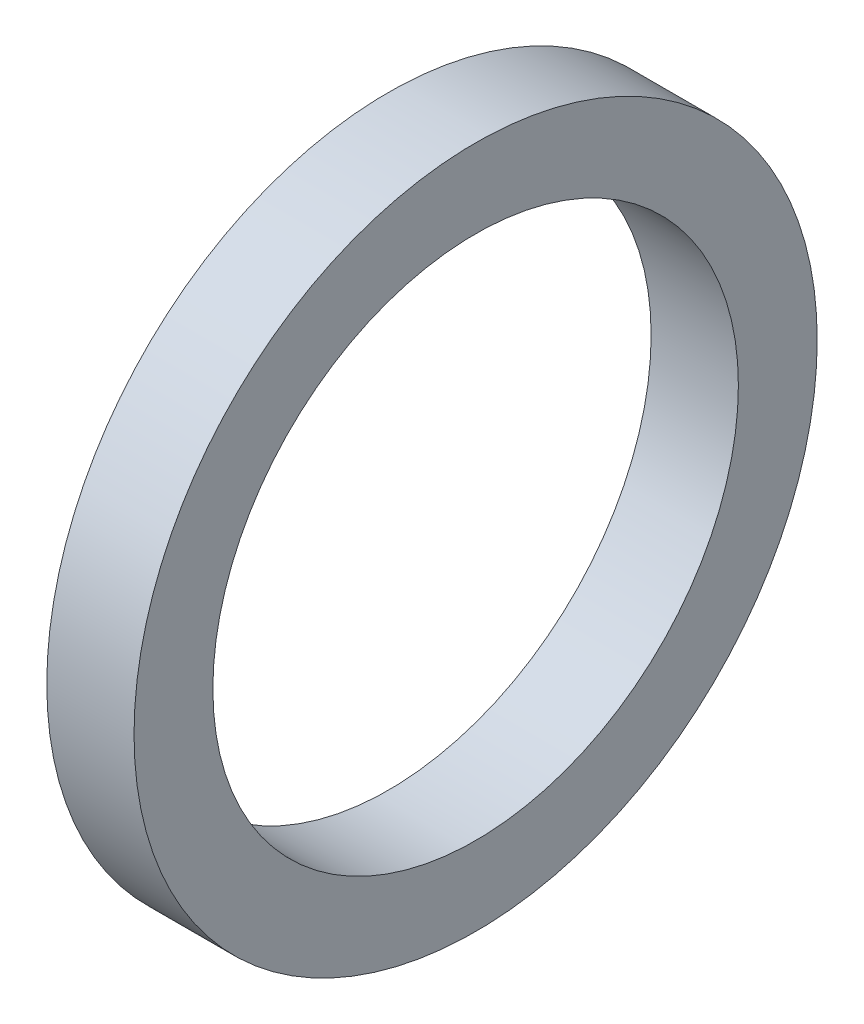
SolidWorks part; units mm, degrees
ref_plane "Front Plane" through (0, 0, 0) normal (0, 0, 1) x (1, 0, 0)
ref_plane "Top Plane" through (0, 0, 0) normal (0, 1, 0) x (1, 0, 0)
ref_plane "Right Plane" through (0, 0, 0) normal (1, 0, 0) x (0, 0, -1)
sketch "Sketch2" plane through (0, 0, 0) normal (0, 0, 1) x (1, 0, 0)
  line L0 (0, 0) -> (58.591, 0) construction
  line L2 (0, 0) -> (18.4, 0)
  line L3 (0, 0) -> (0, 2.5)
  line L4 (0, 2.5) -> (18.4, 2.5)
  line L5 (18.4, 0) -> (18.4, 2.5)
  line L6 (6.0094, 2.5) -> (6.0094, 6)
  line L11 (6.0094, 6) -> (9.9794, 6)
  line L16 (12.9794, 6) -> (12.9794, 3)
  line L17 (12.9794, 3) -> (13.6398, 3)
  line L18 (13.6398, 3) -> (13.6398, 2.5)
  line L19 (13.6398, 2.5) -> (6.0094, 2.5)
  line L22 (13.6398, 2.5) -> (16.1198, 2.5)
  line L23 (13.6398, 2.5) -> (13.6398, 4)
  line L24 (13.6398, 4) -> (16.1198, 4)
  line L25 (16.1198, 2.5) -> (16.1198, 4)
  line L27 (6.0094, 6) -> (9.9794, 6)
  line L28 (6.0094, 6) -> (6.0094, 9)
  line L29 (6.0094, 9) -> (9.9794, 9)
  line L30 (9.9794, 6) -> (9.9794, 9)
  line L31 (6.0094, 9) -> (6.0094, 8.25)
  line L32 (6.0094, 8.25) -> (5.0094, 8.25)
  line L33 (8.6609, 22.001) -> (8.6609, 12.476) construction
  line L34 (5.0094, 12.476) -> (12.3124, 12.476)
  line L35 (9.9794, 9) -> (12.3124, 9)
  line L36 (5.0094, 7.9375) -> (1.7709, 7.9375)
  line L37 (5.0094, 8.25) -> (5.0094, 12.476)
  line L38 (5.0094, 7.9375) -> (5.0094, 13.9365)
  line L39 (5.0094, 13.9365) -> (1.7709, 13.9365)
  line L40 (1.7709, 7.9375) -> (1.7709, 13.9365)
  line L41 (5.0094, 22.001) -> (12.3124, 22.001)
  line L42 (5.0094, 22.001) -> (5.0094, 30.1625)
  line L43 (5.0094, 30.1625) -> (12.3124, 30.1625)
  line L44 (12.3124, 22.001) -> (12.3124, 30.1625)
  line L49 (16.6398, 22.001) -> (16.6398, 7.5)
  line L51 (23.0198, 7.5) -> (23.0198, 6.5)
  line L54 (16.1198, 4) -> (13.6398, 4)
  line L56 (18.0398, 7.5) -> (23.0198, 7.5)
  line L57 (13.3124, 22.001) -> (16.6398, 22.001)
  line L58 (16.1198, 3.5) -> (20.0198, 3.5)
  line L59 (29.9098, 14) -> (26.9098, 11)
  line L60 (4.0094, 31.75) -> (18.0398, 31.75)
  line L61 (18.0398, 7.5) -> (23.0198, 7.5)
  line L62 (18.0398, 7.5) -> (18.0398, 12)
  line L63 (18.0398, 12) -> (23.0198, 12)
  line L64 (23.0198, 7.5) -> (23.0198, 12)
  line L65 (18.0398, 31.75) -> (18.0398, 12)
  line L66 (23.0198, 11) -> (26.9098, 11)
  line L67 (34.8098, 23) -> (31.3098, 19.5)
  line L68 (35.8098, 31) -> (38.7998, 33.99)
  line L69 (29.9098, 14) -> (29.9098, 15)
  line L70 (29.9098, 15) -> (22.9398, 15)
  line L71 (22.9398, 15) -> (21.0398, 15)
  line L72 (18.0398, 7.5) -> (16.6398, 7.5)
  line L73 (21.0398, 15) -> (21.0398, 43)
  line L74 (19.6115, 40) -> (9.6516, 40)
  line L75 (9.6516, 40) -> (4.0094, 40)
  line L76 (21.0398, 43) -> (19.6115, 43)
  line L77 (22.9398, 15) -> (29.9098, 15)
  line L78 (22.9398, 15) -> (22.9398, 21)
  line L79 (22.9398, 21) -> (29.9098, 21)
  line L80 (29.9098, 15) -> (29.9098, 21)
  line L81 (9.6516, 40) -> (19.6115, 40)
  line L82 (9.6516, 40) -> (9.6516, 50)
  line L83 (9.6516, 50) -> (19.6115, 50)
  line L84 (19.6115, 40) -> (19.6115, 50)
  line L85 (4.0094, 40) -> (4.0094, 31.75)
  line L86 (12.9794, 3) -> (12.9794, 2.5)
  line L87 (31.3098, 19.5) -> (29.9098, 19.5)
  line L88 (21.4694, 63.5) -> (21.4694, 51.308)
  line L89 (21.4694, 63.5) -> (25.9398, 63.5)
  line L90 (25.9398, 63.5) -> (25.9398, 25)
  line L91 (27.8398, 25) -> (25.9398, 25)
  line L92 (9.6516, 48) -> (8.2233, 48)
  line L93 (8.2233, 48) -> (8.2233, 53.476)
  line L94 (8.2233, 53.476) -> (19.6115, 53.476)
  line L95 (19.6115, 53.476) -> (19.6115, 50)
  line L96 (13.9174, 63.001) -> (13.9174, 53.476) construction
  line L97 (8.2233, 63.001) -> (19.6115, 63.001)
  line L98 (8.2233, 63.001) -> (8.2233, 68.2625)
  line L99 (8.2233, 68.2625) -> (19.6115, 68.2625)
  line L100 (19.6115, 63.001) -> (19.6115, 68.2625)
  line L101 (12.9794, 6) -> (11.9794, 6)
  line L102 (8.2233, 44.825) -> (4.9848, 44.825)
  line L103 (8.2233, 44.825) -> (8.2233, 54.9365)
  line L104 (8.2233, 54.9365) -> (4.9848, 54.9365)
  line L106 (9.9794, 6) -> (10.8794, 6)
  line L107 (27.8398, 25) -> (34.8098, 25)
  line L108 (34.8098, 25) -> (34.8098, 23)
  line L109 (0, 0) -> (-2, 0)
  line L110 (0, 0) -> (0, 11)
  line L111 (27.8398, 25) -> (34.8098, 25)
  line L112 (27.8398, 25) -> (27.8398, 32.5)
  line L113 (27.8398, 32.5) -> (34.8098, 32.5)
  line L114 (34.8098, 25) -> (34.8098, 32.5)
  line L115 (35.8098, 31) -> (34.8098, 31)
  line L116 (27.8398, 32.5) -> (27.8398, 64.5)
  line L117 (20.5849, 74.025) -> (6.2499, 74.025)
  line L118 (6.2499, 74.025) -> (6.2499, 76.2)
  line L119 (38.7998, 47.29) -> (30.8398, 55.25)
  line L120 (0, 11) -> (-2, 11)
  line L121 (38.7998, 43.815) -> (30.8623, 43.815)
  line L123 (-4.8152, 69.85) -> (1.5348, 76.2)
  line L124 (38.7998, 47.29) -> (38.7998, 33.99)
  line L125 (-2, 0) -> (-2, 11)
  line L126 (38.7998, 37.465) -> (30.8623, 37.465)
  line L127 (30.8623, 43.815) -> (30.8623, 37.465)
  line L128 (6.0094, 2.5) -> (6.0094, 0)
  line L129 (-0.0152, 63.5) -> (-0.0152, 30)
  line L132 (4.9848, 63.5) -> (-0.0152, 63.5)
  line L136 (-1.8152, 30) -> (-11.7752, 30)
  line L138 (-13.7752, 25.4) -> (-2, 25.4)
  line L139 (-2, 25.4) -> (-2, 11.5)
  line L140 (27.8398, 64.5) -> (20.5849, 64.5)
  line L141 (-1.8152, 30) -> (-11.7752, 30)
  line L142 (-1.8152, 30) -> (-1.8152, 39)
  line L143 (-1.8152, 39) -> (-11.7752, 39)
  line L144 (-11.7752, 30) -> (-11.7752, 39)
  line L145 (20.5849, 64.5) -> (20.5849, 74.025)
  line L146 (-12.7752, 37) -> (-12.7752, 47.29)
  line L147 (-12.7752, 37) -> (-11.7752, 37)
  line L148 (30.8398, 55.25) -> (30.8398, 76.2)
  line L149 (11.9794, 6) -> (11.9794, 5.45)
  line L154 (-2, 11.5) -> (0.5, 11.5)
  line L155 (4.9848, 60.6197) -> (24.0348, 60.6197)
  line L160 (4.9848, 60.6197) -> (4.9848, 55.8572)
  line L161 (4.9848, 55.8572) -> (24.0348, 55.8572)
  line L166 (24.0348, 60.6197) -> (24.0348, 55.8572)
  line L167 (4.9848, 60.6197) -> (24.0348, 55.8572) construction
  line L172 (4.9848, 55.8572) -> (24.0348, 60.6197) construction
  line L173 (24.0348, 62.2072) -> (25.9398, 62.2072)
  line L174 (11.9794, 5.45) -> (10.8794, 5.45)
  line L175 (10.8794, 6) -> (10.8794, 5.45)
  line L176 (24.0348, 62.2072) -> (24.0348, 54.2697)
  line L177 (24.0348, 54.2697) -> (25.9398, 54.2697)
  line L178 (25.9398, 62.2072) -> (25.9398, 54.2697)
  line L179 (24.0348, 62.2072) -> (25.9398, 54.2697) construction
  line L180 (24.0348, 54.2697) -> (25.9398, 62.2072) construction
  line L181 (3, 19.6197) -> (15.7, 19.6197)
  line L182 (3, 19.6197) -> (3, 14.8572)
  line L183 (3, 14.8572) -> (15.7, 14.8572)
  line L184 (15.7, 19.6197) -> (15.7, 14.8572)
  line L185 (3, 19.6197) -> (15.7, 14.8572) construction
  line L186 (3, 14.8572) -> (15.7, 19.6197) construction
  line L187 (15.7, 21.2072) -> (16.6398, 21.2072)
  line L188 (15.7, 21.2072) -> (15.7, 13.2697)
  line L189 (15.7, 13.2697) -> (16.6398, 13.2697)
  line L190 (16.6398, 21.2072) -> (16.6398, 13.2697)
  line L191 (15.7, 21.2072) -> (16.6398, 13.2697) construction
  line L192 (15.7, 13.2697) -> (16.6398, 21.2072) construction
  line L193 (0.5, 11.5) -> (0.5, 6.9375)
  line L194 (0.5, 6.9375) -> (1.7709, 6.9375)
  line L195 (23.0198, 6.5) -> (20.0198, 3.5)
  line L196 (4.9848, 63.5) -> (4.9848, 54.9365)
  line L197 (3, 43.825) -> (4.9848, 43.825)
  line L198 (1.7709, 6.9375) -> (1.7709, 7.9375)
  line L199 (6.0094, 0) -> (12.9794, 0)
  line L200 (12.9794, 0) -> (12.9794, 2.5)
  line L201 (18.0398, 31.75) -> (18.0398, 35.875)
  line L202 (18.0398, 35.875) -> (21.0398, 35.875)
  line L203 (30.8398, 76.2) -> (6.2499, 76.2)
  line L204 (2.8049, 69.85) -> (7.2499, 69.85) construction
  line L205 (7.2499, 67.4688) -> (26.2999, 67.4688)
  line L206 (7.2499, 74.025) -> (7.2499, 64.5)
  line L207 (7.2499, 64.5) -> (-1.8152, 64.5)
  line L208 (-1.8152, 64.5) -> (-1.8152, 39)
  line L209 (-12.7752, 47.29) -> (-4.8152, 55.25)
  line L210 (-4.8152, 55.25) -> (-4.8152, 69.85)
  line L211 (7.2499, 67.4688) -> (7.2499, 72.2312)
  line L212 (7.2499, 72.2312) -> (26.2999, 72.2313)
  line L213 (26.2999, 67.4688) -> (26.2999, 72.2313)
  line L214 (26.2999, 73.8187) -> (30.8398, 73.8187)
  line L215 (26.2999, 73.8187) -> (26.2999, 65.8813)
  line L216 (26.2999, 65.8813) -> (30.8398, 65.8813)
  line L217 (30.8398, 73.8187) -> (30.8398, 65.8813)
  line L218 (2.8049, 72.2313) -> (25.0299, 72.2313)
  line L219 (2.8049, 72.2313) -> (2.8049, 67.4687)
  line L220 (2.8049, 67.4687) -> (25.0299, 67.4687)
  line L221 (25.0299, 72.2313) -> (25.0299, 67.4687)
  line L222 (25.0299, 69.85) -> (20.5849, 69.85) construction
  line L223 (21.4694, 51.308) -> (22.9398, 51.308)
  line L224 (22.9398, 51.308) -> (22.9398, 21)
  line L225 (13.6398, 4) -> (13.6398, 12.2697)
  line L226 (13.6398, 12.2697) -> (13.3124, 12.2697)
  line L227 (13.3124, 12.2697) -> (13.3124, 22.001)
  line L228 (12.3124, 9) -> (12.3124, 12.476)
  line L229 (-1.8152, 30) -> (-0.0152, 30)
  line L230 (8.2233, 65.6317) -> (2.8049, 65.6317) construction
  line L231 (19.6115, 65.6317) -> (25.0299, 65.6317) construction
  line L232 (1.5348, 76.2) -> (6.2499, 76.2)
  line L233 (-11.7752, 30) -> (-13.7752, 30)
  line L234 (-13.7752, 30) -> (-13.7752, 25.4)
  line L235 (3, 13.9365) -> (3, 43.825)
  line L236 (4.9848, 54.9365) -> (4.9848, 44.825)
  line L237 (4.9848, 43.825) -> (4.9848, 44.825)
  circle A0 centre (26.8898, 25.95) radius 0.95
  circle A1 centre (21.9898, 15.95) radius 0.95
  circle A2 centre (17.3398, 8.2) radius 0.7
  circle A3 centre (10.4294, 6.45) radius 0.45
  circle A4 centre (-0.9152, 30.9) radius 0.9
  point P7 (24.9873, 58.2385)
  point P131 (16.1699, 17.2385)
  point P135 (14.5098, 58.2385)
  point P146 (9.35, 17.2385)
sketch "Sketch3" plane through (0, 0, 0) normal (0, 0, 1) x (1, 0, 0)
  line L0 (-1.8152, 30) -> (-1.8152, 39) construction
  line L1 (-1.8152, 30) -> (-11.7752, 30) construction
  line L2 (-11.7752, 30) -> (-11.7752, 39) construction
  line L3 (-1.8152, 39) -> (-11.7752, 39) construction
  line L4 (-1.8152, 30) -> (-1.8152, 39)
  line L5 (-1.8152, 30) -> (-11.7752, 30)
  line L6 (-11.7752, 30) -> (-11.7752, 39)
  line L7 (-1.8152, 39) -> (-11.7752, 39)
revolve "Revolve1" add sketch "Sketch3" angle 360 about L0
